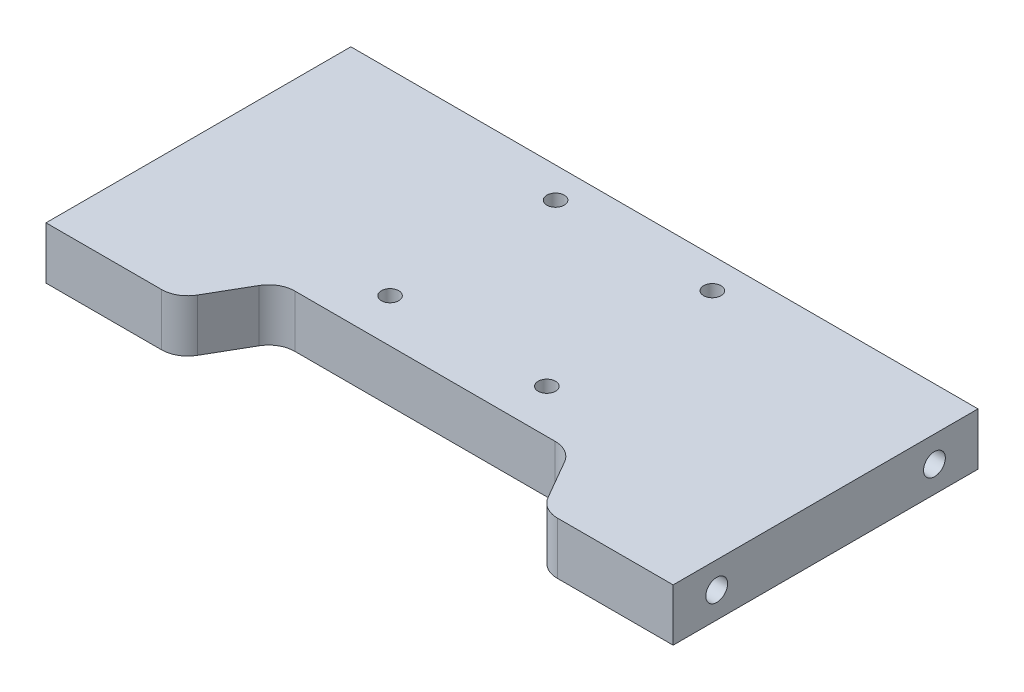
SolidWorks part; units mm, degrees
material "1060 Alloy"
ref_plane "Front Plane" through (0, 0, 0) normal (0, 0, 1) x (1, 0, 0)
ref_plane "Top Plane" through (0, 0, 0) normal (0, 1, 0) x (1, 0, 0)
ref_plane "Right Plane" through (0, 0, 0) normal (1, 0, 0) x (0, 0, -1)
sketch "Sketch1" plane through (0, 0, 0) normal (0, 1, 0) x (1, 0, 0)
  line L1 (0, 0) -> (72, 0)
  line L2 (0, 0) -> (0, 35)
  line L3 (0, 35) -> (72, 35)
  line L4 (72, 0) -> (72, 35)
  dimension "D1" = 72
  dimension "D2" = 35
extrude "Boss-Extrude1" add sketch "Sketch1" along normal blind 6
sketch "Sketch4" plane through (0, 6, 0) normal (0, 1, 0) x (1, 0, 0)
  line L0 (0, 0) -> (72, 0) construction
  line L1 (15, 0) -> (57, 0)
  line L2 (15, 0) -> (19.3301, 7.5)
  line L3 (19.3301, 7.5) -> (52.6699, 7.5)
  line L4 (52.6699, 7.5) -> (57, 0)
  dimension "D5" = 15
  dimension "D4" = 15
  dimension "D1" = 60
  dimension "D2" = 60
  dimension "D3" = 7.5
extrude "Cut-Extrude3" cut sketch "Sketch4" against normal up to next
sketch "Sketch5" plane through (0, 6, 0) normal (0, 1, 0) x (1, 0, 0)
  line L0 (52.6699, 7.5) -> (19.3301, 7.5) construction
  circle A0 centre (27, 12.5) radius 1
  circle A1 centre (45, 12.5) radius 1
  circle A2 centre (45, 31.5) radius 1
  circle A3 centre (27, 31.5) radius 1
  dimension "D3" = 2
  dimension "D4" = 5
  dimension "D1" = 18
  dimension "D2" = 19
  dimension "D5" = 27
extrude "Cut-Extrude4" cut sketch "Sketch5" against normal up to next
fillet "Fillet1" radius 3 4 edges at (57, 3, 0) (52.6699, 3, -7.5) (19.3301, 3, -7.5) (15, 3, 0)
hole_wizard "Tap Drill for M3 Tap1" positions "Sketch7" profile "Sketch6" hole size "M3" standard "ISO"
sketch "Sketch7" plane through (0, 0, 0) normal (-1, 0, 0) x (0, 0, 1)
  line L0 (0, 6) -> (0, 0) construction
  line L1 (-35, 0) -> (0, 0) construction
  point P0 (-30, 3)
  point P2 (-5, 3)
  dimension "D1" = 5
  dimension "D2" = 25
  dimension "D3" = 3
sketch "Sketch6" plane through (0, 3, -30) normal (0, 1, 0) x (0, 0, 1)
  line L0 (0, 0) -> (0, 10.7511)
  line L1 (0, 10.7511) -> (1.25, 10)
  line L2 (1.25, 10) -> (1.25, 0)
  line L5 (1.25, 0) -> (0, 0)
  line L10 (0, 10.7511) -> (-1.25, 10) construction
  line L11 (0, -6.35) -> (0, 107.95) construction
  dimension "Hole Dia." = 2.5
  dimension "Hole Depth" = 10
  dimension "Drill Angle" = 118
hole_wizard "Tap Drill for M3 Tap2" positions "Sketch9" profile "Sketch8" hole size "M3" standard "ISO"
sketch "Sketch9" plane through (72, 0, 0) normal (1, 0, 0) x (0, 0, -1)
  line L0 (0, 6) -> (0, 0) construction
  line L1 (0, 0) -> (35, 0) construction
  point P0 (5, 3)
  point P2 (30, 3)
  dimension "D1" = 5
  dimension "D2" = 25
  dimension "D3" = 3
sketch "Sketch8" plane through (72, 3, -5) normal (0, 1, 0) x (0, 0, -1)
  line L0 (0, 0) -> (0, 10.7511)
  line L1 (0, 10.7511) -> (1.25, 10)
  line L2 (1.25, 10) -> (1.25, 0)
  line L5 (1.25, 0) -> (0, 0)
  line L10 (0, 10.7511) -> (-1.25, 10) construction
  line L11 (0, -6.35) -> (0, 107.95) construction
  dimension "Hole Dia." = 2.5
  dimension "Hole Depth" = 10
  dimension "Drill Angle" = 118
